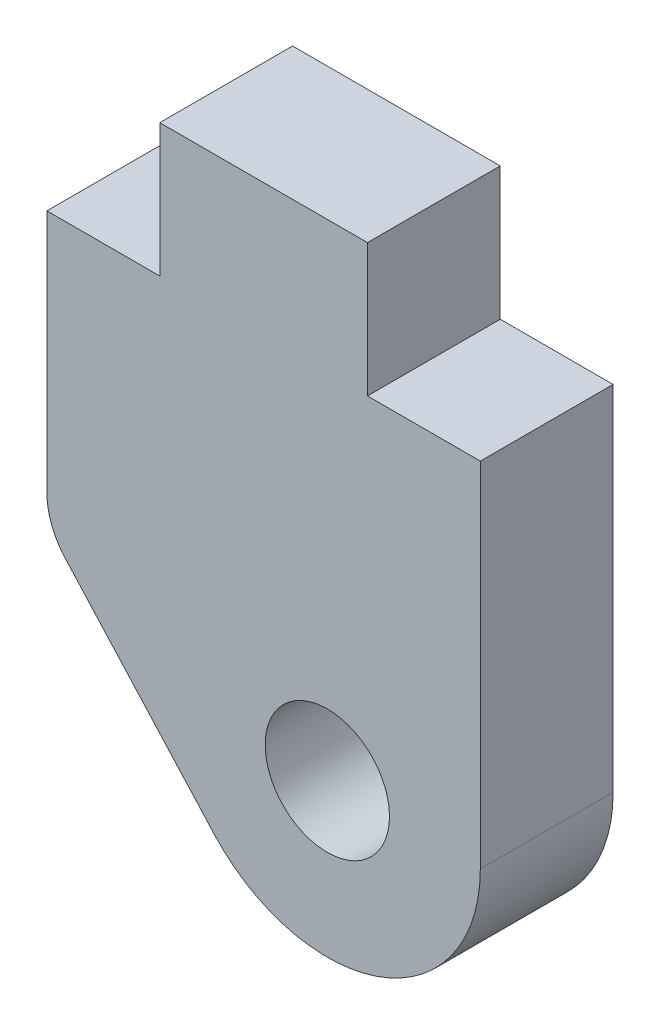
SolidWorks part; units mm, degrees
ref_plane "Front" through (0, 0, 0) normal (0, 0, 1) x (1, 0, 0)
ref_plane "Top" through (0, 0, 0) normal (0, 1, 0) x (1, 0, 0)
ref_plane "Right" through (0, 0, 0) normal (1, 0, 0) x (0, 0, -1)
sketch "Sketch1" plane through (0, 0, 0) normal (0, 0, 1) x (1, 0, 0)
  line L0 (-4.7444, -2.5094) -> (-1.1868, -6.4369)
  line L1 (5.1816, -3.9814) -> (5.1816, 4.4641)
  line L2 (5.1816, 4.4641) -> (2.4828, 4.4641)
  line L3 (2.4828, 4.4641) -> (2.4828, 7.6391)
  line L4 (2.4828, 7.6391) -> (-2.4829, 7.6391)
  line L5 (-2.4829, 7.6391) -> (-2.4829, 4.4641)
  line L6 (-2.4829, 4.4641) -> (-5.1816, 4.4641)
  line L7 (-5.1816, 4.4641) -> (-5.1816, -1.3755)
  arc A0 (-5.1816, -1.3755) -> (-4.7444, -2.5094) centre (-3.4925, -1.3755) ccw
  arc A1 (-1.1868, -6.4369) -> (5.1816, -3.9814) centre (1.524, -3.9814) ccw
  circle A2 centre (1.524, -3.9814) radius 1.4859
extrude "Boss-Extrude1" add sketch "Sketch1" along normal blind 3.175
